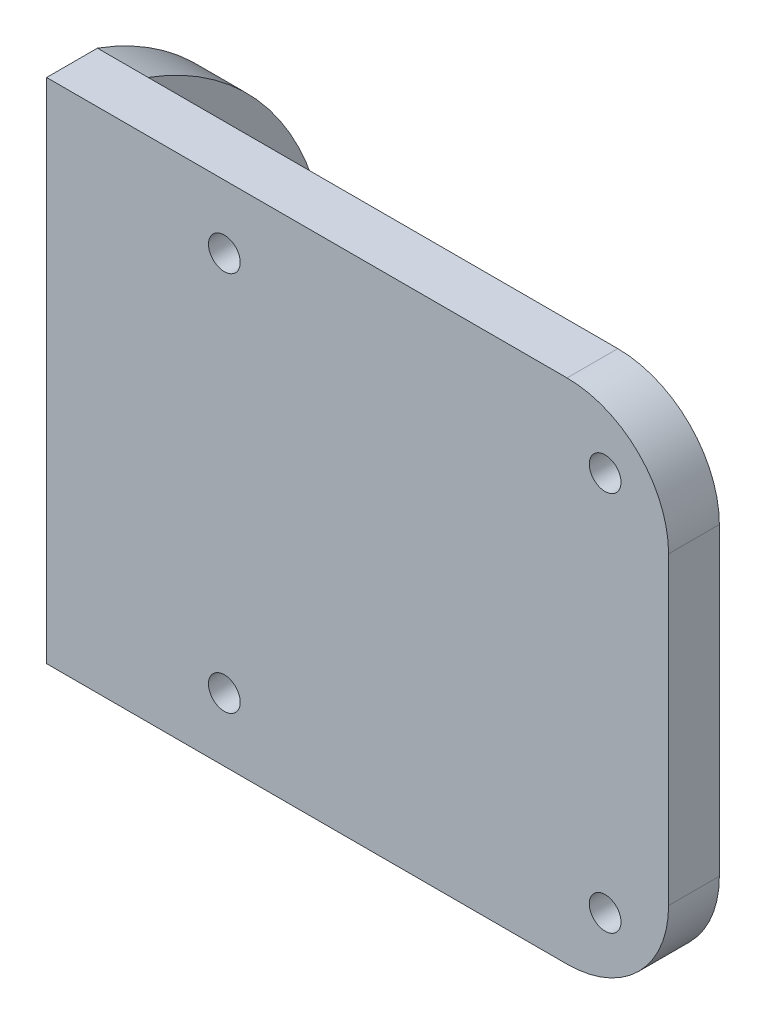
SolidWorks part; units mm, degrees
ref_plane "Front Plane" through (0, 0, 0) normal (0, 0, 1) x (1, 0, 0)
ref_plane "Top Plane" through (0, 0, 0) normal (0, 1, 0) x (1, 0, 0)
ref_plane "Right Plane" through (0, 0, 0) normal (1, 0, 0) x (0, 0, -1)
sketch "Sketch1" plane through (0, 0, 0) normal (1, 0, 0) x (0, 0, -1)
  line L1 (-10, -10) -> (10, -10)
  line L2 (-10, -10) -> (-10, 10)
  line L3 (-10, 10) -> (10, 10)
  line L4 (10, -10) -> (10, 10)
  line L5 (-10, -10) -> (10, 10) construction
  line L6 (-10, 10) -> (10, -10) construction
  point P0 (0, 0)
  dimension "D1" = 20
  dimension "D2" = 20
extrude "Boss-Extrude1" add sketch "Sketch1" along normal blind 4
sketch "Sketch2" plane through (4, 0, 0) normal (1, 0, 0) x (0, 0, -1)
  line L0 (0, -4.5) -> (0, 0) construction
  line L1 (0, 0) -> (0, 4.5) construction
  line L2 (-4.5, 0) -> (0, 0) construction
  line L3 (0, 0) -> (4.5, 0) construction
  circle A0 centre (-4.5, 0) radius 1.1
  circle A1 centre (4.5, 0) radius 1.1
  circle A2 centre (0, 4.5) radius 1.1
  circle A3 centre (0, -4.5) radius 1.1
  dimension "D1" = 2.2
  dimension "D2" = 2.2
  dimension "D3" = 2.2
  dimension "D4" = 2.2
  dimension "D5" = 9
  dimension "D6" = 9
extrude "Cut-Extrude1" cut sketch "Sketch2" against normal through all
sketch "Sketch3" plane through (4, 0, 0) normal (1, 0, 0) x (0, 0, -1)
  line L0 (-10, 10) -> (-10, -10) construction
  line L1 (-10, 20) -> (-6, 20)
  line L2 (-10, 20) -> (-10, -20)
  line L3 (-10, -20) -> (-6, -20)
  line L4 (-6, 20) -> (-6, -20)
  line L6 (0, 0) -> (-6, 0) construction
  line L7 (-6, 0) -> (-10, 0) construction
  point P5 (-6, 0)
  dimension "D1" = 4
  dimension "D2" = 40
extrude "Boss-Extrude2" add sketch "Sketch3" along normal blind 45
sketch "Sketch4" plane through (0, 0, 10) normal (0, 0, 1) x (1, 0, 0)
  line L1 (49, 20) -> (4, 20) construction
  line L2 (49, 20) -> (49, -20) construction
  circle A0 centre (14, 15) radius 1.25
  circle A1 centre (14, -15) radius 1.25
  circle A2 centre (44, 15) radius 1.25
  circle A3 centre (44, -15) radius 1.25
  dimension "D1" = 2.5
  dimension "D2" = 2.5
  dimension "D3" = 2.5
  dimension "D4" = 2.5
  dimension "D9" = 5
  dimension "D5" = 5
  dimension "D6" = 30
  dimension "D7" = 30
  dimension "D8" = 30
extrude "Cut-Extrude2" cut sketch "Sketch4" against normal blind 10
sketch "Sketch5" plane through (4, 0, 0) normal (-1, 0, 0) x (0, 0, 1)
  line L1 (6, -20) -> (10, -20)
  line L2 (6, -20) -> (6, -10)
  line L3 (6, -10) -> (10, -10)
  line L4 (10, -20) -> (10, -10)
  line L5 (10, 10) -> (6, 10)
  line L6 (10, 10) -> (10, 20)
  line L7 (10, 20) -> (6, 20)
  line L8 (6, 10) -> (6, 20)
extrude "Boss-Extrude4" add sketch "Sketch5" along normal blind 4
sketch "Sketch6" plane through (0, 0, 0) normal (-1, 0, 0) x (0, 0, 1)
  line L0 (6, -10) -> (-10, -10) construction
  line L1 (-10, 10) -> (6, 10)
  line L2 (-10, 10) -> (-10, 20)
  line L3 (-10, 20) -> (6, 20)
  line L4 (6, 10) -> (6, 20)
  line L5 (6, -20) -> (-10, -20)
  line L6 (6, -20) -> (6, -10)
  line L7 (6, -10) -> (-10, -10)
  line L8 (-10, -20) -> (-10, -10)
  line L9 (-10, -10) -> (-10, 10) construction
extrude "Boss-Extrude5" add sketch "Sketch6" against normal blind 4
sketch "Sketch7" plane through (0, 0, 0) normal (-1, 0, 0) x (0, 0, 1)
  line L0 (10, 20) -> (-10, 20) construction
  line L1 (10, -20) -> (6, -20)
  line L2 (10, -20) -> (10, 20)
  line L3 (10, 20) -> (6, 20)
  line L4 (6, -20) -> (6, 20)
  line L6 (6, 20) -> (6, -20)
  line L7 (6, 20) -> (-10, 20)
  line L9 (6, 20) -> (6, -20)
  line L10 (6, -20) -> (-10, -20)
  line L11 (-10, 20) -> (-10, -20)
  arc A0 (6, -20) -> (6, 20) centre (13.2914, 0) cw
  line M6 (-10, 20) -> (-10, -20)
  line M7 (-10, -20) -> (10, -20)
  line M9 (10, 20) -> (-10, 20)
  dimension "D2" = 21.2877
  dimension "D1" = 4
extrude "Cut-Extrude3" cut sketch "Sketch7" against normal blind 4 contours A0 M7 M9 M6
fillet "Fillet6" radius 8 2 edges at (49, -20, 8) (49, 20, 8)
